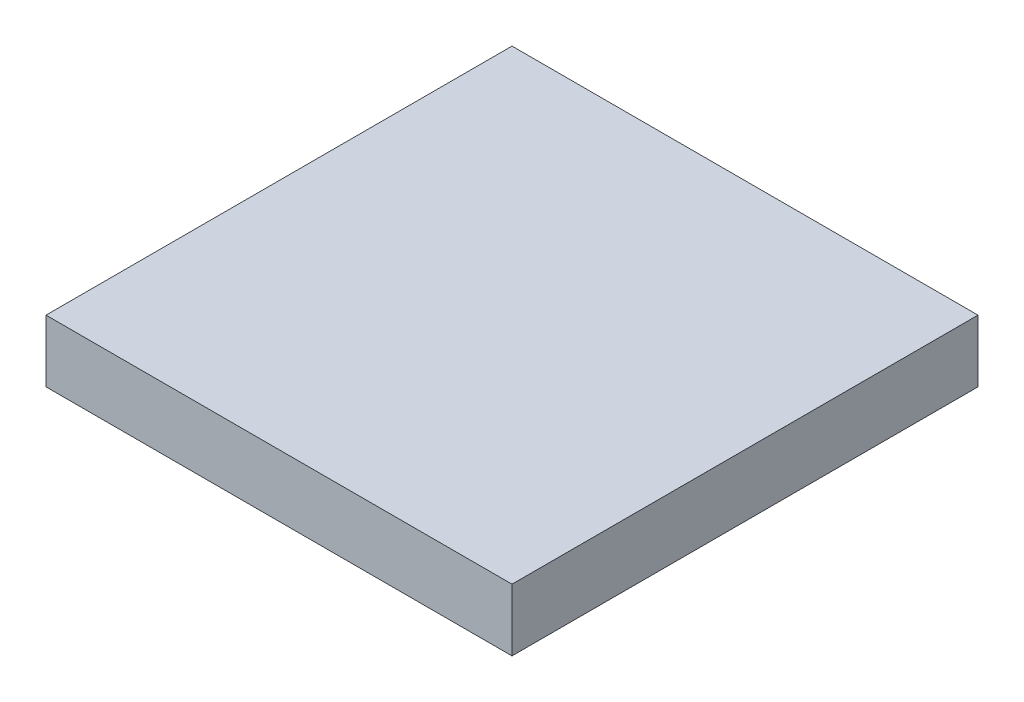
SolidWorks part; units mm, degrees
ref_plane "Front Plane" through (0, 0, 0) normal (0, 0, 1) x (1, 0, 0)
ref_plane "Top Plane" through (0, 0, 0) normal (0, 1, 0) x (1, 0, 0)
ref_plane "Right Plane" through (0, 0, 0) normal (1, 0, 0) x (0, 0, -1)
sketch "Sketch1" plane through (0, 0, 0) normal (0, 1, 0) x (1, 0, 0)
  line L1 (7.5, -7.5) -> (-7.5, -7.5)
  line L2 (7.5, -7.5) -> (7.5, 7.5)
  line L3 (7.5, 7.5) -> (-7.5, 7.5)
  line L4 (-7.5, -7.5) -> (-7.5, 7.5)
  line L5 (7.5, -7.5) -> (-7.5, 7.5) construction
  line L6 (7.5, 7.5) -> (-7.5, -7.5) construction
  point P0 (0, 0)
  point P5 (0, 0)
  dimension "D1" = 15
extrude "Boss-Extrude1" add sketch "Sketch1" along normal blind 2
